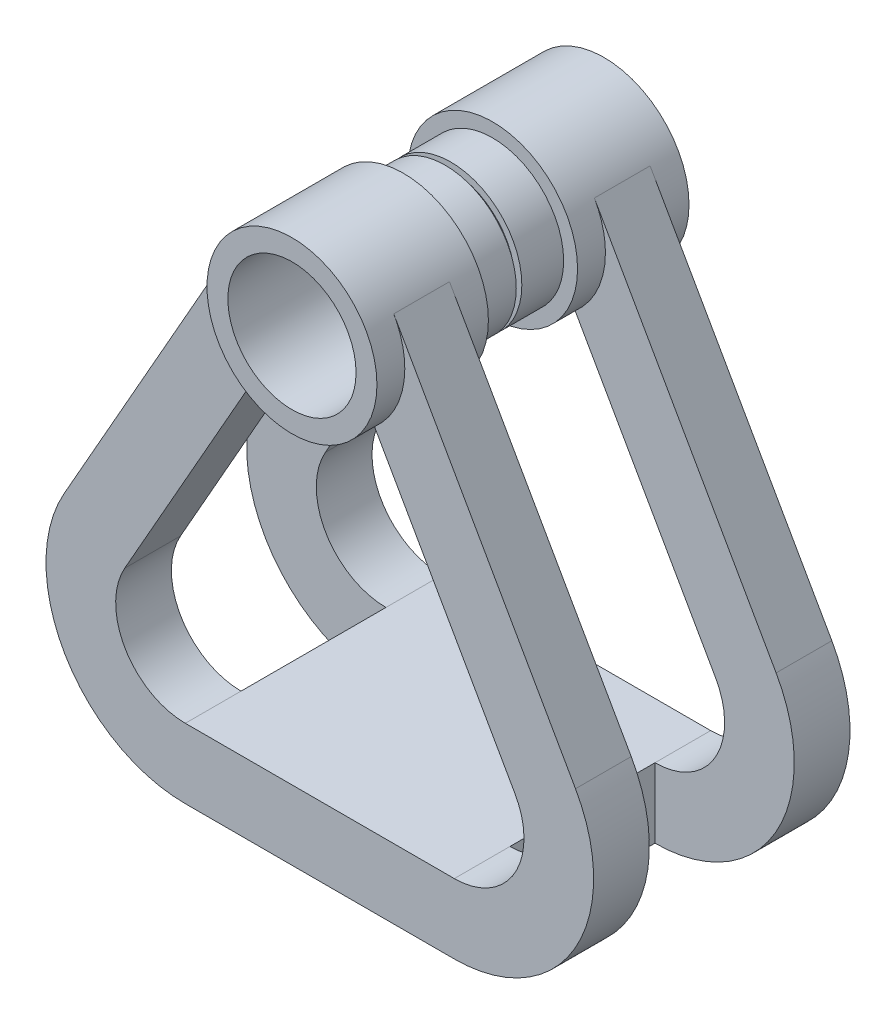
SolidWorks part; units mm, degrees
ref_plane "Front Plane" through (0, 0, 0) normal (0, 0, 1) x (1, 0, 0)
ref_plane "Top Plane" through (0, 0, 0) normal (0, 1, 0) x (1, 0, 0)
ref_plane "Right Plane" through (0, 0, 0) normal (1, 0, 0) x (0, 0, -1)
sketch "Sketch1" plane through (0, 0, 0) normal (0, 0, 1) x (1, 0, 0)
  circle A0 centre (0, 0) radius 4.85
  dimension "D1" = 9.7
extrude "Extrude-Thin1" add sketch "Sketch1" along normal blind 11 thin thin type mid plane wall 0.5
sketch "Sketch2" plane through (0, 0, 11) normal (0, 0, 1) x (1, 0, 0)
  circle A0 centre (0, 0) radius 5.1
  circle A1 centre (0, 0) radius 6.1
  dimension "D1" = 1
extrude "Boss-Extrude2" add sketch "Sketch2" against normal blind 8
ref_plane "Plane1" through (0, 0, 7) normal (0, 0, 1) x (1, 0, 0)
sketch "Sketch3" plane through (0, 0, 7) normal (0, 0, 1) x (1, 0, 0)
  line L0 (5.3056, 3.0101) -> (18.3519, -19.9857)
  line L1 (9.6542, -34.9203) -> (-9.6542, -34.9203)
  line L2 (0, -6.05) -> (0, 6.05) construction
  line L3 (-5.3056, 3.0101) -> (-18.3519, -19.9857)
  line L4 (3.9175, -4.6758) -> (14.0031, -22.453)
  line L5 (9.6542, -29.9203) -> (-9.6542, -29.9203)
  line L6 (-3.9175, -4.6758) -> (-14.0031, -22.453)
  line L7 (-0.9568, 0.5428) -> (-14.0031, -22.453) construction
  line L8 (0.9568, 0.5428) -> (14.0031, -22.453) construction
  arc A0 (-5.3056, 3.0101) -> (-3.9175, -4.6758) centre (0, 0) ccw
  arc A1 (-18.3519, -19.9857) -> (-9.6542, -34.9203) centre (-9.6542, -24.9203) ccw
  arc A2 (18.3519, -19.9857) -> (9.6542, -34.9203) centre (9.6542, -24.9203) cw
  arc A3 (14.0031, -22.453) -> (9.6542, -29.9203) centre (9.6542, -24.9203) cw
  arc A4 (-14.0031, -22.453) -> (-9.6542, -29.9203) centre (-9.6542, -24.9203) ccw
  arc A5 (3.9175, -4.6758) -> (5.3056, 3.0101) centre (0, 0) ccw
  point P9 (0, -34.9203)
  point P12 (-26.8248, -34.9203)
  point P15 (26.8248, -34.9203)
  dimension "D1" = 10
  dimension "D2" = 5
extrude "Boss-Extrude3" add sketch "Sketch3" along normal blind 2 and the other way blind 2
ref_plane "Plane2" through (0, 0, -0.2) normal (0, 0, -1) x (-1, 0, 0)
sketch "Sketch4" plane through (0, 0, -0.2) normal (0, 0, -1) x (-1, 0, 0)
  line L1 (-9.6542, -29.9203) -> (9.6542, -29.9203)
  line L2 (-9.6542, -29.9203) -> (-9.6542, -34.9203)
  line L3 (-9.6542, -34.9203) -> (9.6542, -34.9203)
  line L4 (9.6542, -29.9203) -> (9.6542, -34.9203)
extrude "Boss-Extrude4" add sketch "Sketch4" against normal up to surface (5.2 mm away) up to face at (0, -18.8244, 5)
mirror "Mirror3" about plane through (0, 0, -0.2) normal (0, 0, -1) of bodies 105
